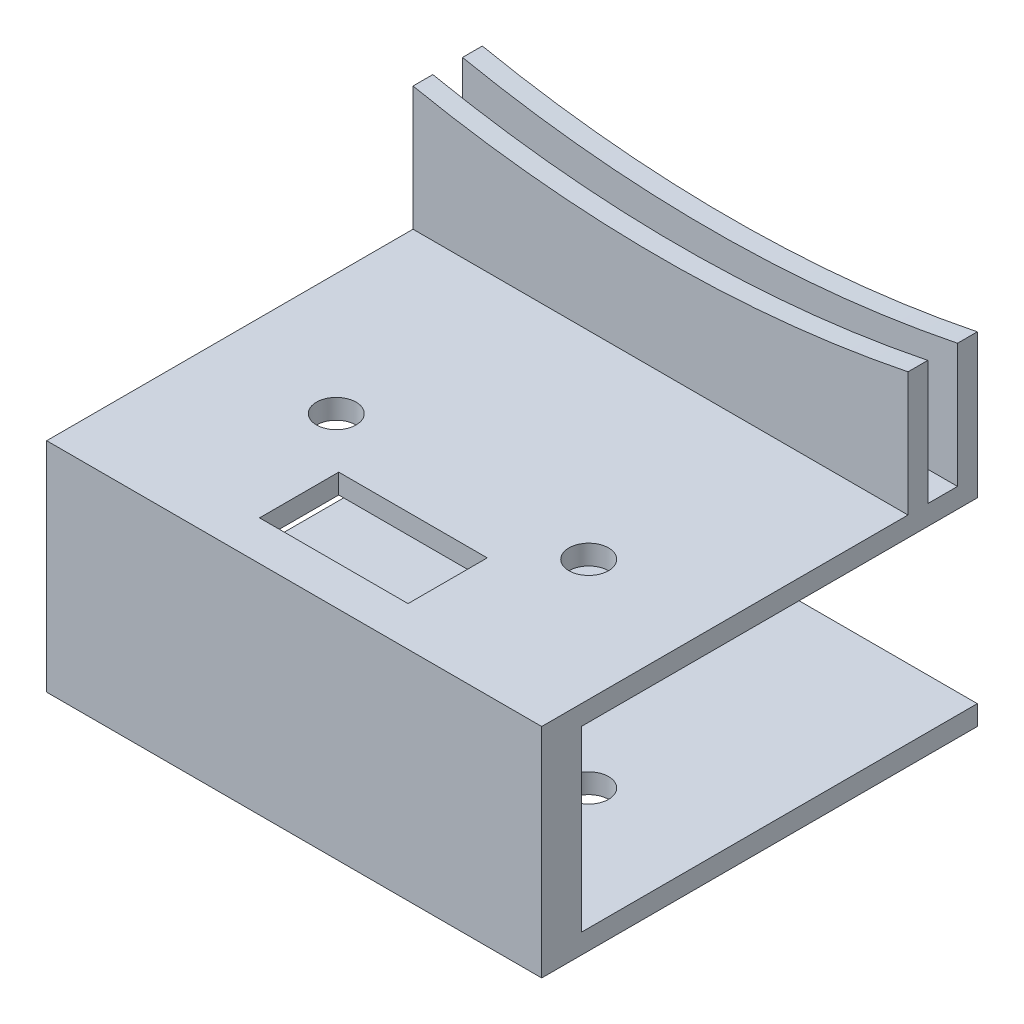
SolidWorks part; units mm, degrees
ref_plane "정면" through (0, 0, 0) normal (0, 0, 1) x (1, 0, 0)
ref_plane "윗면" through (0, 0, 0) normal (0, 1, 0) x (1, 0, 0)
ref_plane "우측면" through (0, 0, 0) normal (1, 0, 0) x (0, 0, -1)
sketch "스케치1" plane through (0, 0, 0) normal (0, 1, 0) x (1, 0, 0)
  line L1 (-25, 22) -> (25, 22)
  line L2 (-25, 22) -> (-25, -22)
  line L3 (-25, -22) -> (25, -22)
  line L4 (25, 22) -> (25, -22)
  line L5 (-25, 22) -> (25, -22) construction
  line L6 (-25, -22) -> (25, 22) construction
  point P0 (0, 0)
  dimension "D1" = 50
  dimension "D2" = 44
extrude "보스-돌출1" add sketch "스케치1" along normal blind 22
sketch "스케치2" plane through (0, 22, 0) normal (0, 1, 0) x (1, 0, 0)
  line L0 (25, -22) -> (25, 22) construction
  line L1 (-25, 22) -> (25, 22)
  line L2 (-25, 22) -> (-25, 20)
  line L3 (-25, 20) -> (25, 20)
  line L4 (25, 22) -> (25, 20)
  line L5 (-25, 22) -> (-25, -22) construction
  line L6 (-25, 17) -> (25, 17)
  line L7 (-25, 17) -> (-25, 15)
  line L8 (-25, 15) -> (25, 15)
  line L9 (25, 17) -> (25, 15)
  dimension "D1" = 2
  dimension "D2" = 2
  dimension "D3" = 3
extrude "보스-돌출2" add sketch "스케치2" along normal blind 20
sketch "스케치3" plane through (25, 0, 0) normal (1, 0, 0) x (0, 0, -1)
  line L0 (22, 42) -> (22, 0) construction
  line L1 (22, 20) -> (-18, 20)
  line L2 (22, 20) -> (22, 2)
  line L3 (22, 2) -> (-18, 2)
  line L4 (-18, 20) -> (-18, 2)
  line L5 (-22, 0) -> (22, 0) construction
  line L6 (15, 42) -> (15, 22) construction
  dimension "D1" = 18
  dimension "D2" = 2
  dimension "D3" = 33
extrude "컷-돌출1" cut sketch "스케치3" against normal blind 50
sketch "스케치4" plane through (0, 0, 0) normal (0, -1, 0) x (1, 0, 0)
  line L0 (25, 18) -> (-25, 18) construction
  line L1 (25, 22) -> (25, -22) construction
  line L2 (-25, -22) -> (-25, 22) construction
  line L3 (25, -22) -> (-25, -22) construction
  line L4 (25, 5) -> (-25, 5) construction
  circle A0 centre (12.75, 5) radius 2
  circle A1 centre (-12.75, 5) radius 2
  dimension "D3" = 4
  dimension "D4" = 4
  dimension "D1" = 40
  dimension "D2" = 13
  dimension "D5" = 12.25
  dimension "D6" = 12.25
extrude "컷-돌출2" cut sketch "스케치4" against normal blind 22
sketch "스케치5" plane through (0, 22, 0) normal (0, 1, 0) x (1, 0, 0)
  line L0 (25, -22) -> (25, 15) construction
  line L1 (-7.5, -10) -> (7.5, -10)
  line L2 (-7.5, -10) -> (-7.5, -18)
  line L3 (-7.5, -18) -> (7.5, -18)
  line L4 (7.5, -10) -> (7.5, -18)
  line L6 (-25, -22) -> (25, -22) construction
  dimension "D1" = 15
  dimension "D2" = 8
  dimension "D3" = 17.5
  dimension "D4" = 4
extrude "컷-돌출3" cut sketch "스케치5" against normal blind 2
sketch "스케치7" plane through (0, 0, -22) normal (0, 0, -1) x (-1, 0, 0)
  line L0 (0, 20) -> (0, 61.3353) construction
  line L5 (25, 20) -> (-25, 20) construction
  line L6 (25, 42) -> (25, 20) construction
  line L7 (-25, 42) -> (-25, 20) construction
  line L8 (25, 34.5255) -> (25, 42)
  line L9 (25, 42) -> (-25, 42)
  line L10 (-25, 42) -> (-25, 34.5255)
  arc A0 (25, 34.5255) -> (-25, 34.5255) centre (0, 157) cw
  dimension "D2" = 125
  dimension "D1" = 137
  dimension "D3" = 0
  dimension "D4" = 0
  dimension "D5" = 7.4745
extrude "컷-돌출4" cut sketch "스케치7" against normal blind 7
